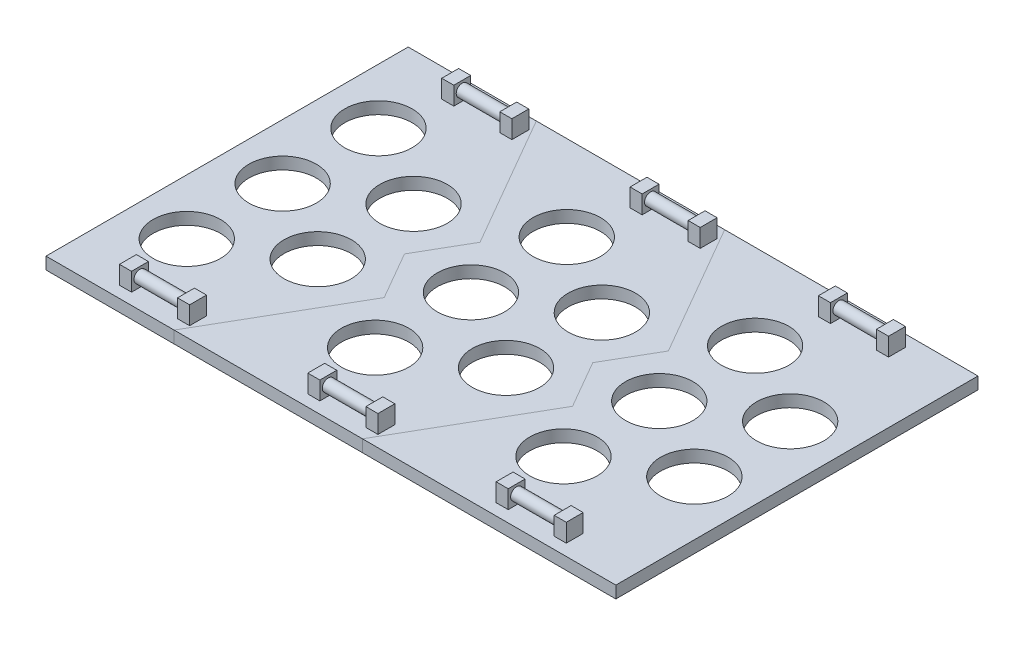
SolidWorks part; units mm, degrees
ref_plane "Front Plane" through (0, 0, 0) normal (0, 0, 1) x (1, 0, 0)
ref_plane "Top Plane" through (0, 0, 0) normal (0, 1, 0) x (1, 0, 0)
ref_plane "Right Plane" through (0, 0, 0) normal (1, 0, 0) x (0, 0, -1)
sketch "Sketch1" plane through (0, 0, 0) normal (0, 1, 0) x (1, 0, 0)
  line L0 (-118, 0) -> (118, 0)
  line L1 (-118, -75) -> (-118, 75)
  line L2 (118, -75) -> (118, 75)
  line L3 (-118, 75) -> (118, 75)
  line L4 (118, -75) -> (-118, -75)
  point P4 (0, 0)
  point P8 (-118, 0)
  point P11 (118, 0)
  dimension "D1" = 236
  dimension "D2" = 150
  dimension "D3" = 150
extrude "Boss-Extrude1" add sketch "Sketch1" along normal mid plane 5 contours L4 L2 L0 L1 | L3 L1 L0 L2
sketch "Sketch4" plane through (0, 2.5, 0) normal (0, 1, 0) x (1, 0, 0)
  line L0 (-118, -75) -> (-118, 75) construction
  circle A0 centre (-95, 0) radius 13.97
  circle A1 centre (-95, 0) radius 17.907
  circle A2 centre (-95, -39.6875) radius 13.97
  circle A3 centre (-95, -39.6875) radius 17.907
  circle A4 centre (-95, 39.6875) radius 13.97
  circle A5 centre (-95, 39.6875) radius 17.907
  circle A6 centre (-60.6296, 19.8437) radius 13.97
  circle A7 centre (-60.6296, 19.8437) radius 17.907
  circle A8 centre (-60.6296, -19.8437) radius 17.907
  circle A9 centre (-60.6296, -19.8437) radius 13.97
  dimension "D1" = 27.94
  dimension "D2" = 35.814
  dimension "D3" = 19.8438
  dimension "D4" = 19.8437
  dimension "D5" = 19.8437
  dimension "D6" = 19.8438
  dimension "D7" = 23
extrude "Cut-Extrude1" cut sketch "Sketch4" against normal blind 10.4 contours A2 | A0 | A9 | A6 | A4
pattern_linear "LPattern1" count 3 spacing 78 along (1, 0, 0) of "Cut-Extrude1"
sketch "Sketch10" plane through (0, 2.5, 0) normal (0, 1, 0) x (1, 0, 0)
  line L0 (-95, -66.7375) -> (-60.6296, -66.7375) construction
  line L1 (118, -75) -> (-118, -75) construction
  line L2 (-87.3398, -66.7375) -> (-68.2898, -66.7375)
  line L3 (-87.3398, -70.2375) -> (-87.3398, -63.2375)
  line L4 (-87.3398, -63.2375) -> (-92.3398, -63.2375)
  line L5 (-92.3398, -63.2375) -> (-92.3398, -70.2375)
  line L6 (-92.3398, -70.2375) -> (-87.3398, -70.2375)
  line L7 (-68.2898, -70.2375) -> (-68.2898, -63.2375)
  line L8 (-68.2898, -63.2375) -> (-63.2898, -63.2375)
  line L9 (-63.2898, -63.2375) -> (-63.2898, -70.2375)
  line L10 (-63.2898, -70.2375) -> (-68.2898, -70.2375)
  circle A0 centre (-60.6296, -19.8437) radius 13.97 construction
  circle A1 centre (-95, -39.6875) radius 13.97 construction
  point P13 (-77.8148, -66.7375)
  point P14 (-87.3398, -66.7375)
  point P19 (-68.2898, -66.7375)
  dimension "D1" = 8.2625
  dimension "D2" = 19.05
  dimension "D3" = 7
  dimension "D4" = 5
extrude "Boss-Extrude2" add sketch "Sketch10" along normal blind 7.5 contours L0 L5 L6 L3 | L5 L0 L3 L4 | L7 L0 L9 L8
sketch "Sketch11" plane through (-87.3398, 0, 0) normal (1, 0, 0) x (0, 0, -1)
  line L0 (-70.2375, 10) -> (-66.7375, 10) construction
  line L1 (-66.7375, 10) -> (-66.7375, 6.5) construction
  circle A0 centre (-66.7375, 6.5) radius 2.5
  dimension "D2" = 5
  dimension "D1" = 3.5
extrude "Boss-Extrude3" add sketch "Sketch11" along normal up to surface (19.05 mm away) up to face at (-68.2898, 6.25, 66.7375)
mirror "Mirror1" about plane through (0, 0, 0) normal (0, 0, 1) of "Boss-Extrude2", "Boss-Extrude3"
pattern_linear "LPattern2" count 3 spacing 78 along (1, 0, 0) of "Mirror1", "Boss-Extrude2", "Boss-Extrude3"
sketch "Sketch9" plane through (0, 2.5, 0) normal (0, 1, 0) x (1, 0, 0)
  line L12 (-39.9722, 31.7703) -> (-33.0864, 19.8437)
  line L13 (-39.9722, 7.9172) -> (-33.0864, 19.8437)
  line L14 (-39.9722, 7.9172) -> (-44.5432, 0)
  line L18 (-39.7318, -8.3336) -> (-44.5432, 0)
  line L19 (-35.5384, -24.0908) -> (-33.0864, -19.8438)
  line L20 (-39.7318, -8.3336) -> (-33.0864, -19.8438)
  line L22 (-39.9722, 31.7703) -> (-64.9309, 75)
  line L23 (-118, 75) -> (118, 75) construction
  line L24 (-35.5384, -24.0908) -> (-64.9309, -75)
  line L25 (118, -75) -> (-118, -75) construction
  line L43 (41.9696, 24.9429) -> (13.0691, 75)
  line L44 (41.9696, 24.9429) -> (44.9136, 19.8438)
  line L45 (38.0278, 7.9172) -> (44.9136, 19.8438)
  line L46 (38.0278, 7.9172) -> (33.4568, 0)
  line L47 (33.4568, 0) -> (43.527, -17.4422)
  line L48 (43.527, -17.4422) -> (44.9136, -19.8437)
  line L49 (38.0278, -31.7703) -> (13.0691, -75)
  line L50 (44.9136, -19.8437) -> (38.0278, -31.7703)
split "Split1" trim tools "Sketch9" bodies to split 121 resulting bodies 122 123 124
delete or keep bodies "Body-Delete/Keep 1" [suppressed] type delete bodies bodies 123 122
delete or keep bodies "Body-Delete/Keep 2" [suppressed] type delete bodies bodies 123 124
delete or keep bodies "Body-Delete/Keep 3" [suppressed] type delete bodies bodies 122 124
